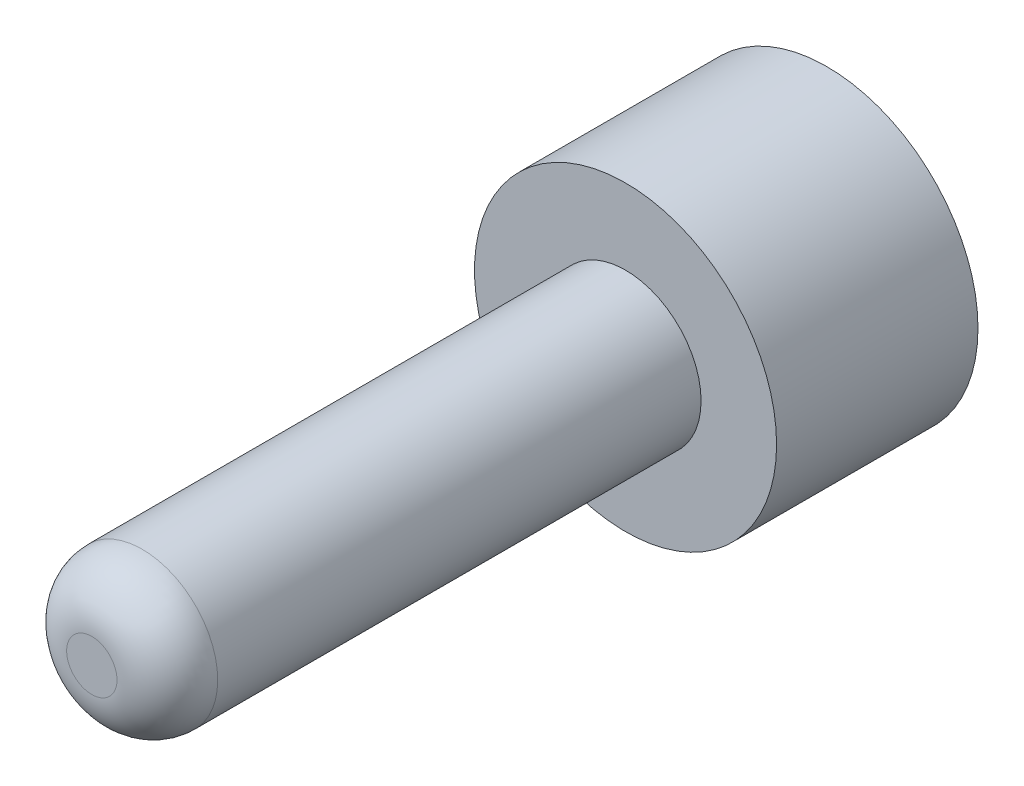
SolidWorks part; units mm, degrees
ref_plane "Front Plane" through (0, 0, 0) normal (0, 0, 1) x (1, 0, 0)
ref_plane "Top Plane" through (0, 0, 0) normal (0, 1, 0) x (1, 0, 0)
ref_plane "Right Plane" through (0, 0, 0) normal (1, 0, 0) x (0, 0, -1)
sketch "Sketch1" plane through (0, 0, 0) normal (0, 0, 1) x (1, 0, 0)
  circle A0 centre (0, 0) radius 1.5
  dimension "D1" = 3
extrude "Boss-Extrude1" add sketch "Sketch1" along normal blind 2
sketch "Sketch2" plane through (0, 0, 2) normal (0, 0, 1) x (1, 0, 0)
  circle A0 centre (0, 0) radius 0.75
  dimension "D1" = 1.5
extrude "Boss-Extrude2" add sketch "Sketch2" along normal blind 5.3
fillet "Fillet1" radius 0.5 1 edges at (0.75, 0, 7.3)
